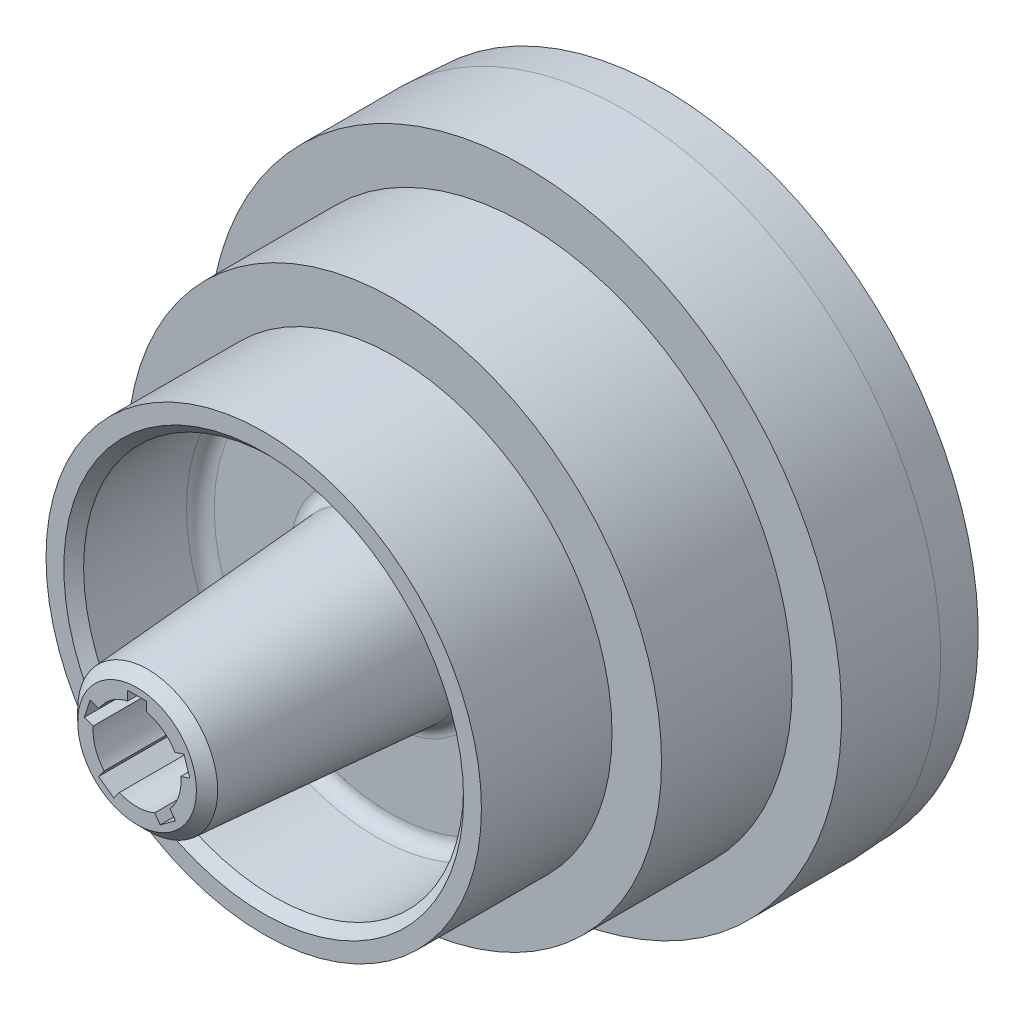
SolidWorks part; units mm, degrees
material "ABS"
ref_plane "Front Plane" through (0, 0, 0) normal (0, 0, 1) x (1, 0, 0)
ref_plane "Top Plane" through (0, 0, 0) normal (0, 1, 0) x (1, 0, 0)
ref_plane "Right Plane" through (0, 0, 0) normal (1, 0, 0) x (0, 0, -1)
sketch "Sketch1" plane through (0, 0, 0) normal (0, 1, 0) x (1, 0, 0)
  line L13 (0, 121.2174) -> (0, -88.5217) construction
  line L14 (-11.11, 105) -> (-11.11, 0)
  line L15 (-11.11, 0) -> (-17.5, 0)
  line L16 (-17.5, 0) -> (-22, 64)
  line L17 (-22, 64) -> (-48, 64)
  line L18 (-48, 64) -> (-48, 32)
  line L19 (-48, 32) -> (-55, 32)
  line L20 (-55, 32) -> (-55, 65)
  line L21 (-55, 65) -> (-67.5, 65)
  line L22 (-67.5, 65) -> (-67.5, 98)
  line L23 (-67.5, 98) -> (-80, 98)
  line L24 (-80, 98) -> (-80, 123)
  line L26 (-74, 133) -> (-74, 106)
  line L27 (-74, 106) -> (-61, 106)
  line L28 (-61, 106) -> (-61, 73)
  line L29 (-61, 73) -> (-22, 73)
  line L30 (-22, 73) -> (-17.5, 105)
  line L31 (-17.5, 105) -> (-11.11, 105)
  line L34 (-79.5, 133) -> (-74, 133)
  line L35 (-80, 123) -> (-79.5, 133)
  dimension "D1" = 32
  dimension "D2" = 64
  dimension "D3" = 22.22
  dimension "D4" = 35
  dimension "D5" = 44
  dimension "D6" = 33
  dimension "D7" = 33
  dimension "D8" = 159
  dimension "D9" = 96
  dimension "D10" = 110
  dimension "D11" = 122
  dimension "D12" = 135
  dimension "D13" = 25
  dimension "D14" = 148
  dimension "D15" = 160
  dimension "D16" = 9
  dimension "D17" = 8
  dimension "D18" = 35
  dimension "D19" = 133
revolve "Revolve3" add sketch "Sketch1" angle 360 about L13
chamfer "Chamfer1" distance 2.5 angle 45 4 edges at (-74, 0, -133) (-48, 0, -32) (-17.5, 0, -105) (-17.5, 0, 0)
fillet "Fillet1" radius 3.5 6 edges at (-74, 0, -106) (-61, 0, -106) (-61, 0, -73) (-48, 0, -64) (-22, 0, -73) (-22, 0, -64)
sketch "Sketch2" plane through (0, 0, 0) normal (0, 0, 1) x (1, 0, 0)
  line L6 (-2.38, 10.8521) -> (-2.38, 13.2321)
  line L7 (-2.38, 13.2321) -> (2.38, 13.2321)
  line L8 (2.38, 10.8521) -> (2.38, 13.2321)
  line L9 (-2.38, 10.8521) -> (2.38, 13.2321) construction
  line L10 (-2.38, 13.2321) -> (2.38, 10.8521) construction
  arc A0 (-2.38, 10.8521) -> (2.38, 10.8521) centre (0, 0) ccw
  circle A1 centre (0, 0) radius 11.11 construction
  point P2 (0, 12.0421)
  dimension "D1" = 4.76
  dimension "D2" = 2.38
extrude "Cut-Extrude1" cut sketch "Sketch2" against normal blind 45
pattern_circular "CirPattern1" count 5 over 360 about axis through (0, 0, 0) along (0, 0, 1) of "Cut-Extrude1"
